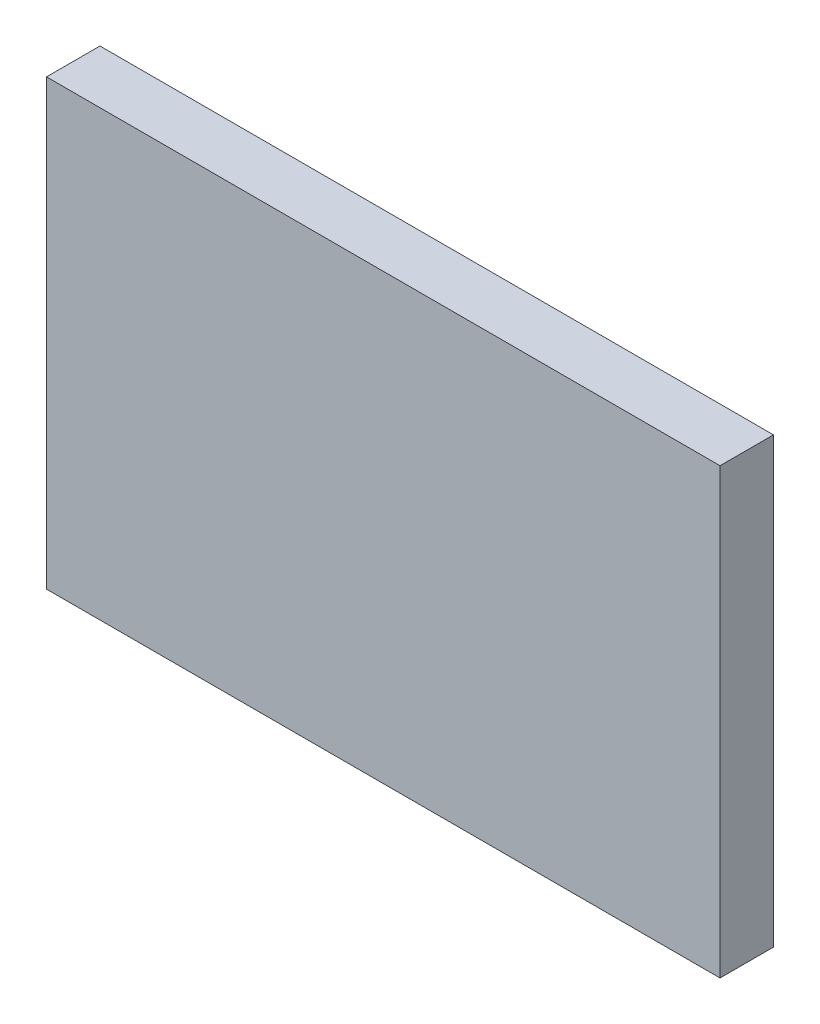
SolidWorks part; units mm, degrees
ref_plane "Front" through (0, 0, 0) normal (0, 0, 1) x (1, 0, 0)
ref_plane "Top" through (0, 0, 0) normal (0, 1, 0) x (1, 0, 0)
ref_plane "Right" through (0, 0, 0) normal (1, 0, 0) x (0, 0, -1)
sketch "Sketch1" plane through (0, 0, 0) normal (0, 0, 1) x (1, 0, 0)
  line L1 (0, 0) -> (12.6, 0)
  line L2 (0, 0) -> (0, -8.3)
  line L3 (0, -8.3) -> (12.6, -8.3)
  line L4 (12.6, 0) -> (12.6, -8.3)
  dimension "D1" = 12.6
  dimension "D2" = 8.3
extrude "Extrude1" add sketch "Sketch1" along normal blind 1
